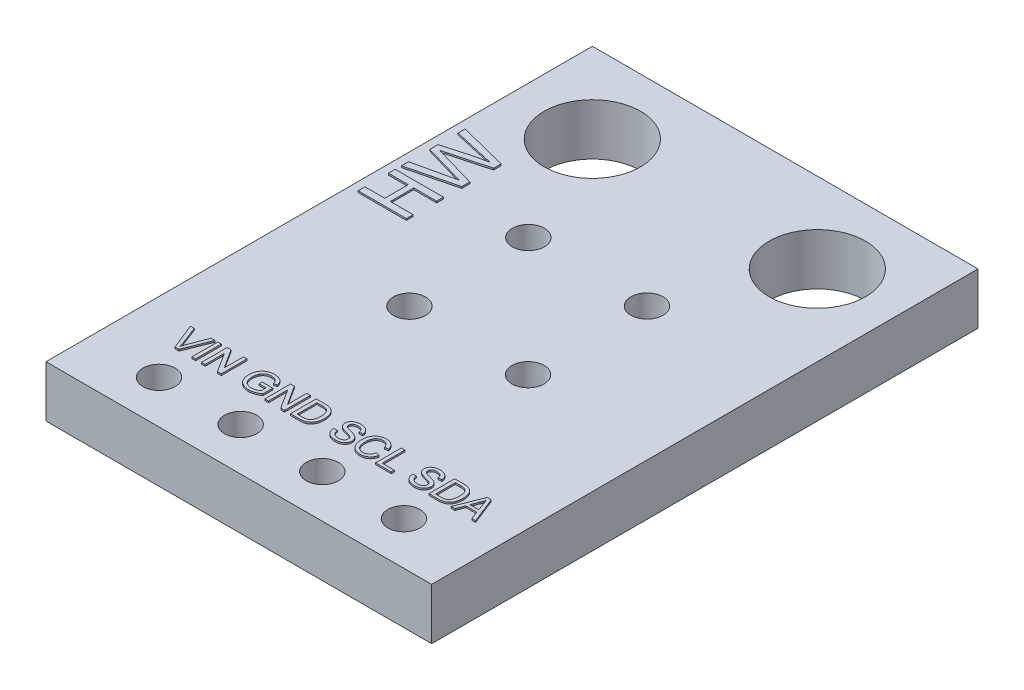
SolidWorks part; units mm, degrees
ref_plane "Спереди" through (0, 0, 0) normal (0, 0, 1) x (1, 0, 0)
ref_plane "Сверху" through (0, 0, 0) normal (0, 1, 0) x (1, 0, 0)
ref_plane "Справа" through (0, 0, 0) normal (1, 0, 0) x (0, 0, -1)
sketch "Эскиз2" plane through (0, 0, 0) normal (0, 1, 0) x (1, 0, 0)
  line L0 (-11.7073, 3.2889) -> (49988.2927, 3.2889) construction
  line L1 (-7.3568, 5.7889) -> (4.6432, 5.7889)
  line L2 (-7.3568, 5.7889) -> (-7.3568, -11.2111)
  line L3 (-7.3568, -11.2111) -> (4.6432, -11.2111)
  line L4 (4.6432, 5.7889) -> (4.6432, -11.2111)
  line L5 (-4.8568, 7.4737) -> (-4.8568, -49992.5263) construction
  line L6 (2.1432, 8.8419) -> (2.1432, -49991.1581) construction
  line L7 (-6.9691, -9.8738) -> (49993.0309, -9.8738) construction
  line L8 (-1.3568, -11.2111) -> (-1.3568, 49988.7889) construction
  line L9 (-10.4575, -2.2111) -> (49989.5425, -2.2111) construction
  line L10 (-9.6853, -0.3611) -> (49990.3147, -0.3611) construction
  line L11 (-9.9261, -4.0611) -> (49990.0739, -4.0611) construction
  line L12 (0.4932, 1.1982) -> (0.4932, -49998.8018) construction
  line L13 (-3.2068, 1.8517) -> (-3.2068, -49998.1483) construction
  circle A0 centre (-4.8568, 3.2889) radius 1.5
  circle A1 centre (2.1432, 3.2889) radius 1.5
  circle A2 centre (-5.1768, -9.8738) radius 0.5
  circle A3 centre (-2.6368, -9.8738) radius 0.5
  circle A4 centre (-0.0968, -9.8738) radius 0.5
  circle A5 centre (2.4432, -9.8738) radius 0.5
  circle A7 centre (-3.1983, -0.3611) radius 0.5
  circle A8 centre (-3.1983, -4.0611) radius 0.5
  circle A9 centre (0.4932, -4.0611) radius 0.5
  circle A10 centre (0.4932, -0.3611) radius 0.5
  point P26 (-1.3568, -11.2111)
  dimension "D6" = 3
  dimension "D7" = 3
  dimension "D8" = 1
  dimension "D9" = 1
  dimension "D10" = 1
  dimension "D11" = 1
  dimension "D12" = 2.54
  dimension "D13" = 2.54
  dimension "D14" = 2.54
  dimension "D15" = 2.2
  dimension "D16" = 9
  dimension "D22" = 1
  dimension "D23" = 1
  dimension "D24" = 1
  dimension "D25" = 1
  dimension "D1" = 12
  dimension "D2" = 17
  dimension "D3" = 2.5
  dimension "D4" = 2.5
  dimension "D5" = 2.5
  dimension "D18" = 1.85
  dimension "D19" = 1.85
  dimension "D20" = 1.85
  dimension "D21" = 1.85
extrude "Бобышка-Вытянуть1" add sketch "Эскиз2" along normal blind 1.6
sketch "Эскиз3" plane through (0, 1.6, 0) normal (0, 1, 0) x (1, 0, 0)
  line L0 (-5.5568, 2.7889) -> (-5.5568, -3.2111) construction
  line L1 (-7.3568, 5.7889) -> (-7.3568, -11.2111) construction
  line L2 (4.6432, 5.7889) -> (-7.3568, 5.7889) construction
  text T0 "VIN GND SCL SDA" font "Arial" height 0.8
  text T1 "HW" font "Arial" height 1.5
  dimension "D1" = 1.8
  dimension "D2" = 3
  dimension "D3" = 9
extrude "Бобышка-Вытянуть2" add sketch "Эскиз3" along normal blind 0.05
sketch "Эскиз4" plane through (0, 0, 0) normal (0, -1, 0) x (1, 0, 0)
  line L0 (4.2432, 4.2774) -> (4.2432, -1.2048) construction
  line L1 (4.6432, 11.2111) -> (4.6432, -5.7889) construction
  text T0 "HW-691" font "Arial" height 1
  dimension "D1" = 0.4
extrude "Бобышка-Вытянуть3" add sketch "Эскиз4" along normal blind 0.01
